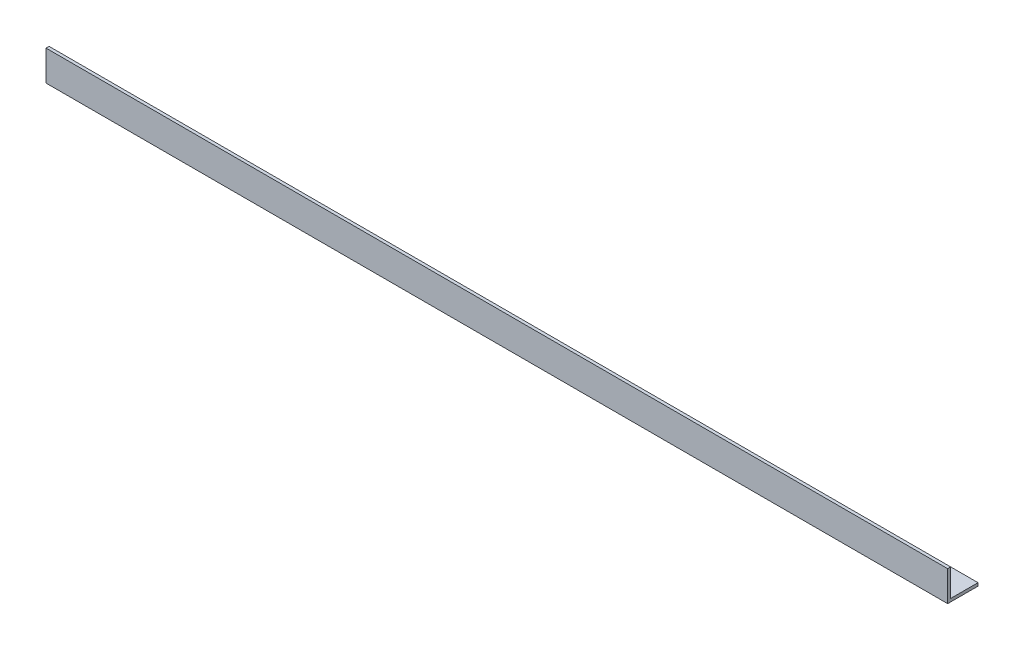
SolidWorks part; units mm, degrees
ref_plane "Спереди" through (0, 0, 0) normal (0, 0, 1) x (1, 0, 0)
ref_plane "Сверху" through (0, 0, 0) normal (0, 1, 0) x (1, 0, 0)
ref_plane "Справа" through (0, 0, 0) normal (1, 0, 0) x (0, 0, -1)
sketch "Эскиз1" plane through (0, 0, 0) normal (1, 0, 0) x (0, 0, -1)
  line L0 (0, 0) -> (0, 15)
  line L1 (0, 15) -> (1.5, 15)
  line L2 (1.5, 15) -> (1.5, 1.5)
  line L3 (1.5, 1.5) -> (15, 1.5)
  line L4 (15, 1.5) -> (15, 0)
  line L5 (15, 0) -> (0, 0)
  dimension "D1" = 15
  dimension "D2" = 15
  dimension "D3" = 1.5
  dimension "D4" = 1.5
extrude "Бобышка-Вытянуть1" add sketch "Эскиз1" along normal blind 446
